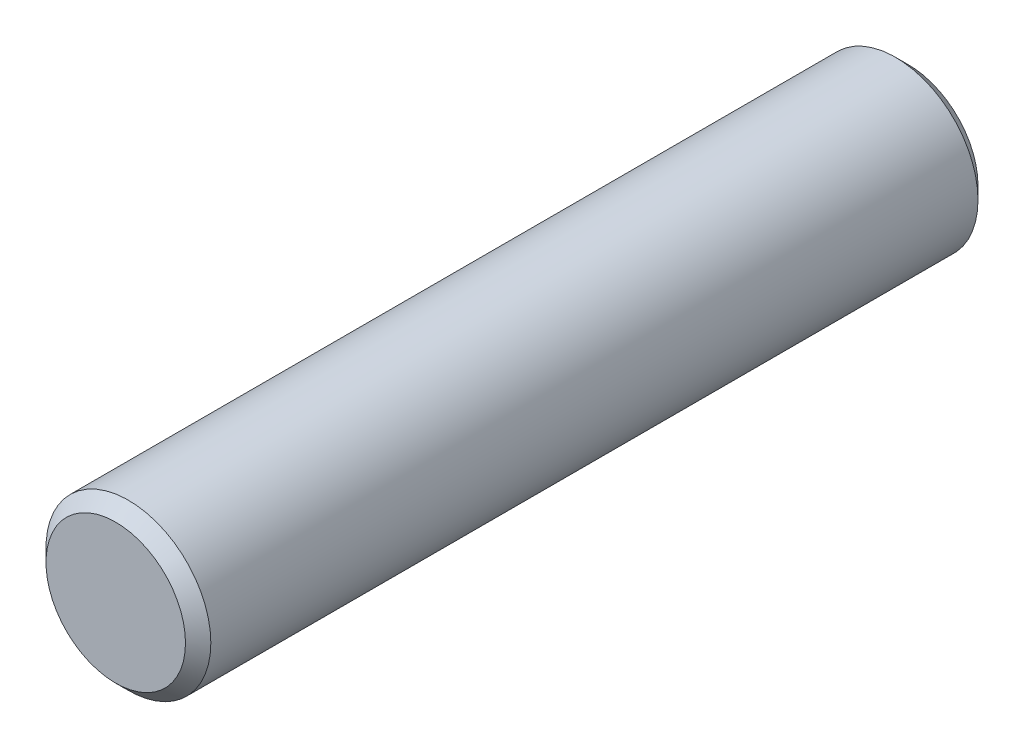
SolidWorks part; units mm, degrees
material "Plain Carbon Steel"
ref_plane "Front Plane" through (0, 0, 0) normal (0, 0, 1) x (1, 0, 0)
ref_plane "Top Plane" through (0, 0, 0) normal (0, 1, 0) x (1, 0, 0)
ref_plane "Right Plane" through (0, 0, 0) normal (1, 0, 0) x (0, 0, -1)
sketch "Sketch1" plane through (0, 0, 0) normal (0, 0, 1) x (1, 0, 0)
  circle A0 centre (0, 0) radius 1.651
  dimension "D1" = 3.302
extrude "Boss-Extrude1" add sketch "Sketch1" along normal mid plane 15.875
chamfer "Chamfer1" distance 0.254 angle 45 2 edges at (1.651, 0, -7.9375) (1.651, 0, 7.9375)
